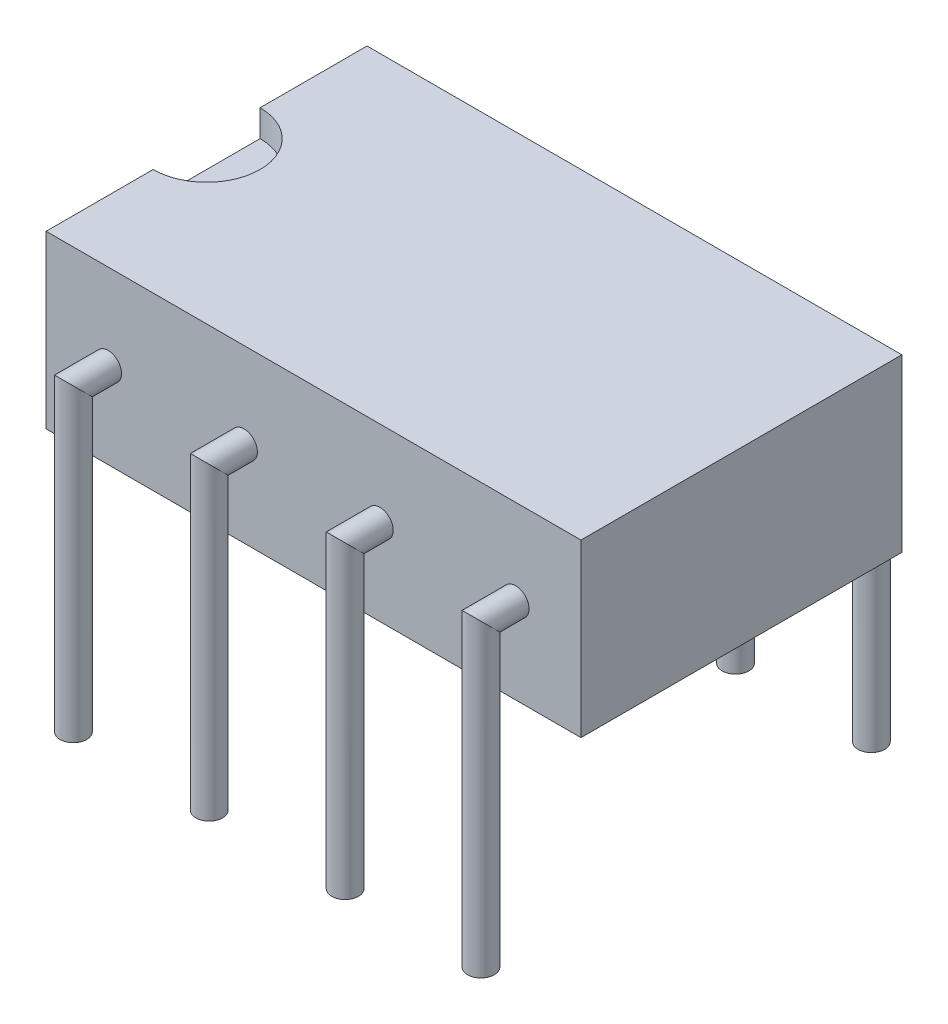
SolidWorks part; units mm, degrees
ref_plane "Plan de face" through (0, 0, 0) normal (0, 0, 1) x (1, 0, 0)
ref_plane "Plan de dessus" through (0, 0, 0) normal (0, 1, 0) x (1, 0, 0)
ref_plane "Plan de droite" through (0, 0, 0) normal (1, 0, 0) x (0, 0, -1)
sketch "Esquisse1" plane through (0, 0, 0) normal (1, 0, 0) x (0, 0, -1)
  line L0 (-34.0084, 0) -> (28.7946, 0) construction
  line L1 (0, -15.76) -> (0, 25.9507) construction
  line L2 (-13.1897, 3.2) -> (13.1184, 3.2) construction
  line L3 (3, 10.112) -> (3, -6.1718) construction
  line L4 (-3, 10.112) -> (-3, -4.99) construction
  line L6 (-3, 3.2) -> (3, 3.2)
  line L7 (-3, 3.2) -> (-3, 0)
  line L8 (-3, 0) -> (3, 0)
  line L9 (3, 3.2) -> (3, 0)
  dimension "D1" = 3
  dimension "D2" = 6
  dimension "D3" = 3.2
extrude "Extrusion1" add sketch "Esquisse1" along normal blind 10
sketch "Esquisse2" plane through (0, 3.2, 0) normal (0, 1, 0) x (-1, 0, 0)
  line L0 (0, -1) -> (0, 1)
  arc A0 (0, 1) -> (0, -1) centre (0, 0) ccw
extrude "Enlèv. mat.-Extru.1" cut sketch "Esquisse2" against normal blind 0.5
sketch "Esquisse3" plane through (0, 0, 3) normal (0, 0, 1) x (1, 0, 0)
  line L0 (-0.9705, 0) -> (10.7632, 0) construction
  line L1 (0, 4.319) -> (0, -1.0907) construction
  line L2 (-0.7349, 1.6) -> (2.3847, 1.6) construction
  line L3 (1.16, 2.698) -> (1.16, -1.0907) construction
  circle A0 centre (1.16, 1.6) radius 0.25
  dimension "D1" = 1.6
  dimension "D2" = 1.16
ref_plane "Plan1" through (1.16, 0, 0) normal (1, 0, 0) x (0, 0, -1)
sketch "Esquisse5" plane through (1.16, 0, 0) normal (1, 0, 0) x (0, 0, -1)
  line L0 (-4.2866, 0) -> (4.976, 0) construction
  line L1 (-3, -1.7147) -> (-3, 5.2592) construction
  line L2 (-4.2866, -4) -> (4.976, -4) construction
  line L3 (-3.65, -4.4343) -> (-3.65, 4.8284) construction
  line L4 (-3.7349, 1.6) -> (-3, 1.6) construction
  line L5 (-3, 1.6) -> (-3.65, 1.6)
  line L6 (-3.65, 1.6) -> (-3.65, -4)
  dimension "D1" = 4
  dimension "D2" = 0.65
sweep "Balayage1" add profiles "Esquisse3" path "Esquisse5"
ref_plane "Plan2" through (0, 0, 0) normal (0, 0, 1) x (1, 0, 0)
mirror "Symétrie1" about plane through (0, 0, 0) normal (0, 0, 1) of "Balayage1"
pattern_linear "Répétition linéaire1" count 4 spacing 2.54 along (1, 0, 0) of "Balayage1", "Symétrie1"
